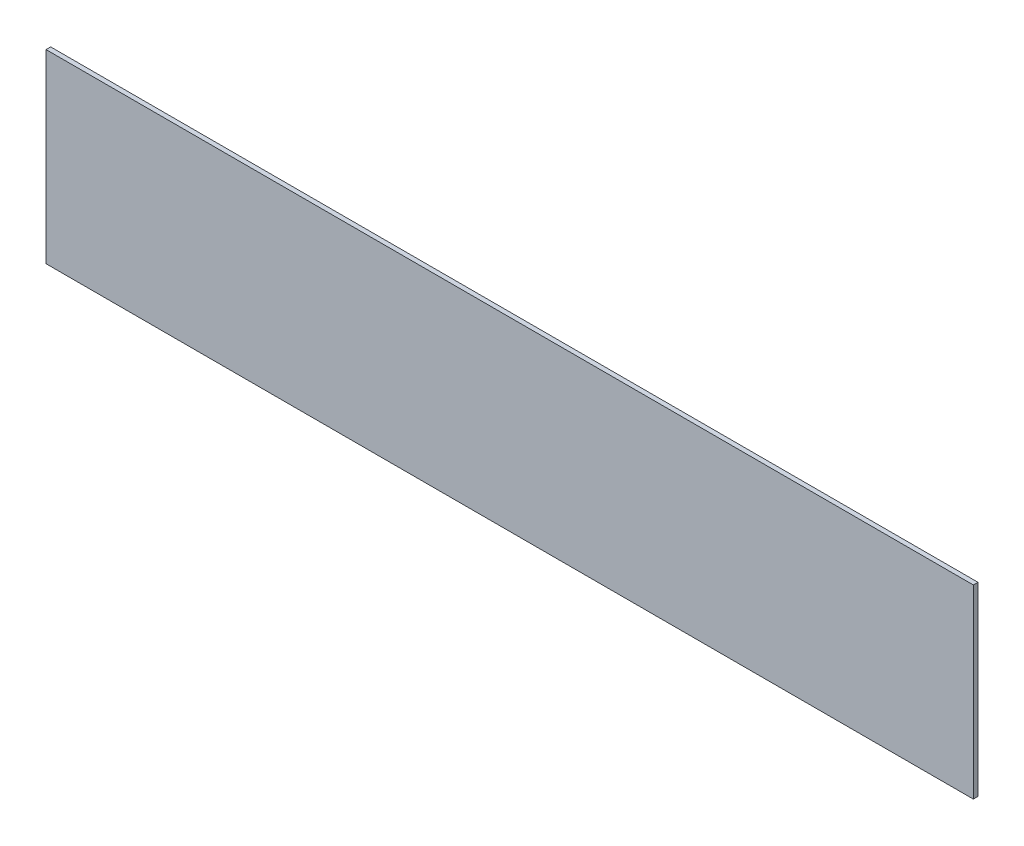
SolidWorks part; units mm, degrees
material "Plain Carbon Steel"
ref_plane "Front Plane" through (0, 0, 0) normal (0, 0, 1) x (1, 0, 0)
ref_plane "Top Plane" through (0, 0, 0) normal (0, 1, 0) x (1, 0, 0)
ref_plane "Right Plane" through (0, 0, 0) normal (1, 0, 0) x (0, 0, -1)
sketch "Sketch1" plane through (0, 0, 0) normal (0, 0, 1) x (1, 0, 0)
  line L1 (245.0787, -30.8858) -> (-54.9213, -30.8858)
  line L2 (245.0787, -30.8858) -> (245.0787, 29.1142)
  line L3 (245.0787, 29.1142) -> (-54.9213, 29.1142)
  line L4 (-54.9213, -30.8858) -> (-54.9213, 29.1142)
  line L5 (245.0787, -30.8858) -> (-54.9213, 29.1142) construction
  line L6 (245.0787, 29.1142) -> (-54.9213, -30.8858) construction
  point P0 (95.0787, -0.8858)
  dimension "D1" = 60
  dimension "D2" = 300
extrude "Boss-Extrude1" add sketch "Sketch1" along normal blind 1.5
